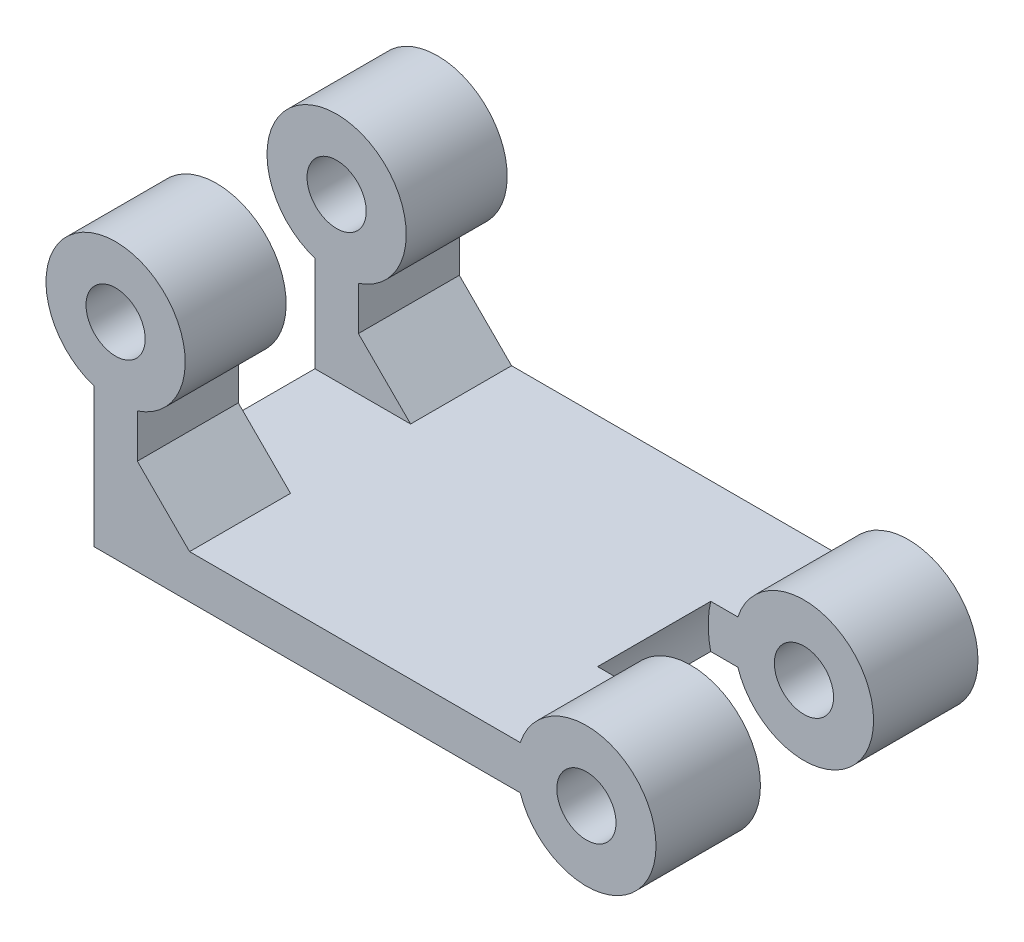
SolidWorks part; units mm, degrees
ref_plane "Спереди" through (0, 0, 0) normal (0, 0, 1) x (1, 0, 0)
ref_plane "Сверху" through (0, 0, 0) normal (0, 1, 0) x (1, 0, 0)
ref_plane "Справа" through (0, 0, 0) normal (1, 0, 0) x (0, 0, -1)
sketch "Эскиз2" plane through (0, 0, 0) normal (0, 0, 1) x (1, 0, 0)
  circle A0 centre (0, 0) radius 4
  circle A1 centre (0, 0) radius 1.7
  dimension "D1" = 3.4
  dimension "D2" = 8
extrude "Бобышка-Вытянуть1" add sketch "Эскиз2" along normal blind 6
pattern_linear "Линейный массив1" count 2 spacing 12.5 along (0, 0, 1) of "Бобышка-Вытянуть1"
sketch "Эскиз3" plane through (0, 0, 0) normal (0, 0, -1) x (-1, 0, 0)
  line L0 (0, 0) -> (13.124, 0) construction
  line L1 (3.7997, 1.25) -> (25.7997, 1.25)
  line L2 (3.7997, 1.25) -> (3.7997, -1.25)
  line L3 (3.7997, -1.25) -> (25.7997, -1.25)
  line L6 (25.7997, -1.25) -> (28.2997, -1.25)
  line L7 (25.7997, 1.25) -> (25.7997, 6.75)
  line L9 (28.2997, -1.25) -> (28.2997, 6.75)
  circle A0 centre (0, 0) radius 4 construction
  arc A1 (28.2997, 6.75) -> (25.7997, 6.75) centre (27.0497, 10.5497) ccw
  circle A2 centre (27.0497, 10.5497) radius 1.7
  point P15 (27.0497, 13.1396)
  point P16 (0, 0)
  point P18 (0, 0)
  dimension "D6" = 8
  dimension "D7" = 3.4
  dimension "D1" = 2.5
  dimension "D2" = 22
  dimension "D3" = 8
  dimension "D4" = 2.5
  dimension "D5" = 3.7997
extrude "Бобышка-Вытянуть2" add sketch "Эскиз3" against normal up to surface (18.5 mm away) up to face at (4, 0, 18.5)
sketch "Эскиз4" plane through (0, 0, 6) normal (0, 0, 1) x (1, 0, 0)
  circle A1 centre (0, 0) radius 5.5
  dimension "D1" = 11
extrude "Вырез-Вытянуть1" cut sketch "Эскиз4" along normal blind 6.5
ref_plane "Плоскость7" through (0, 0, 9.25) normal (0, 0, -1) x (-1, 0, 0)
sketch "Эскиз9" plane through (0, 0, 9.25) normal (0, 0, -1) x (-1, 0, 0)
  line L1 (20.3175, 19.1173) -> (35.2742, 19.1173)
  line L2 (20.3175, 19.1173) -> (20.3175, 1.25)
  line L3 (20.3175, 1.25) -> (35.2742, 1.25)
  line L4 (35.2742, 19.1173) -> (35.2742, 1.25)
extrude "Вырез-Вытянуть3" cut sketch "Эскиз9" along normal blind 3.45
mirror "Зеркальное отражение1" about plane through (0, 0, 9.25) normal (0, 0, -1) of "Вырез-Вытянуть3"
chamfer "Фаска1" distance 3 angle 45 2 edges at (-25.7997, 1.25, 15.6) (-25.7997, 1.25, 2.9)
